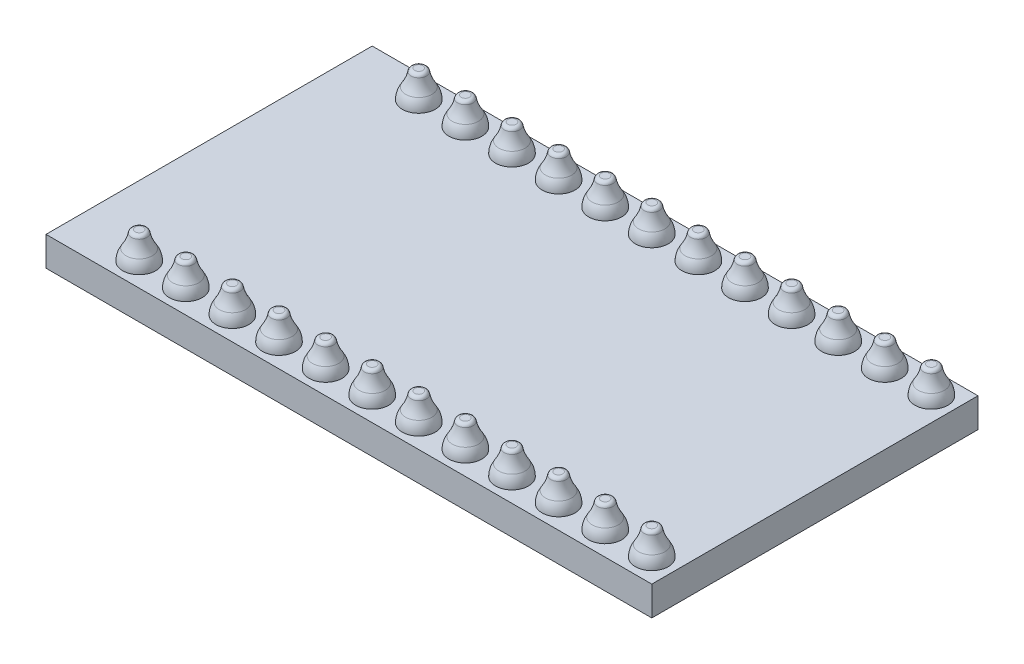
SolidWorks part; units mm, degrees
material "E-Glass Fiber"
ref_plane "Front Plane" through (0, 0, 0) normal (0, 0, 1) x (1, 0, 0)
ref_plane "Top Plane" through (0, 0, 0) normal (0, 1, 0) x (1, 0, 0)
ref_plane "Right Plane" through (0, 0, 0) normal (1, 0, 0) x (0, 0, -1)
sketch "Sketch1" plane through (0, 0, 0) normal (0, 1, 0) x (1, 0, 0)
  line L0 (0, 7.62) -> (-3.81, 7.62) construction
  line L1 (-3.81, 16.51) -> (29.21, 16.51)
  line L2 (-3.81, 16.51) -> (-3.81, -1.27)
  line L3 (-3.81, -1.27) -> (29.21, -1.27)
  line L4 (29.21, 16.51) -> (29.21, -1.27)
  line L5 (0, 0) -> (27.94, 0) construction
  line L6 (0, 0) -> (0, 15.24) construction
  line L7 (0, 15.24) -> (27.94, 15.24) construction
  line L8 (27.94, 0) -> (27.94, 15.24) construction
  line L10 (27.94, 7.62) -> (29.21, 7.62) construction
  dimension "D1" = 33.02
  dimension "D2" = 17.78
  dimension "D3" = 15.24
  dimension "D4" = 27.94
  dimension "D5" = 1.27
extrude "Boss-Extrude2" add sketch "Sketch1" along normal blind 1.6
sketch "Sketch2" plane through (0, 0, 0) normal (0, 1, 0) x (1, 0, 0)
  line L0 (0, -0.88) -> (0, 0.88) construction
  line L2 (-0.88, 0) -> (0.88, 0) construction
  circle A0 centre (0, 0) radius 0.45
  circle A1 centre (0, 15.24) radius 0.45
  dimension "D1" = 0.9
  dimension "D2" = 15.24
extrude "Cut-Extrude2" cut sketch "Sketch2" along normal blind 1.6
pattern_linear "LPattern3" count 12 spacing 2.54 along (1, 0, 0) of "Cut-Extrude2"
sketch "Sketch6" plane through (0, 0, 0) normal (1, 0, 0) x (0, 0, -1)
  line L0 (0, 1.6) -> (0.9, 1.6)
  line L1 (-1.27, 1.6) -> (16.51, 1.6) construction
  line L2 (0.2252, 3.1) -> (0, 3.1)
  line L3 (0, 1.705) -> (0, -1.705) construction
  line L4 (0, 3.1) -> (0, 1.6)
  line L5 (0, 1.3722) -> (0, 3.4408) construction
  arc A0 (0.9, 1.6) -> (0.7139, 2.2122) centre (-0.2, 1.6) ccw
  arc A1 (0.7139, 2.2122) -> (0.4221, 2.9352) centre (2.2924, 3.2697) cw
  arc A2 (0.4221, 2.9352) -> (0.2252, 3.1) centre (0.2252, 2.9) ccw
  point P16 (0.4, 3.1)
  dimension "D4" = 1.1
  dimension "D5" = 1.9
  dimension "D6" = 0.2
  dimension "D1" = 1.5
  dimension "D2" = 0.8
  dimension "D3" = 1.8
revolve "Revolve1" add sketch "Sketch6" angle 360 about L5
pattern_linear "LPattern2" count 2 spacing 15.24 along (0, 0, -1) count 12 spacing 2.54 along (1, 0, 0) of "Revolve1"
ref_plane "Plane3" through (0, 0, -5.08) normal (0, 0, 1) x (1, 0, 0)
sketch "Sketch9" plane through (0, 0, 0) normal (0, 1, 0) x (1, 0, 0)
  line L0 (-1.705, 0) -> (1.705, 0) construction
  line L2 (-3.81, 16.51) -> (-3.81, -1.27) construction
  circle A0 centre (-0.06, 5.725) radius 0.4
  circle A1 centre (-0.06, 9.475) radius 0.4
  dimension "D1" = 0.8
  dimension "D2" = 3.75
  dimension "D3" = 5.725
  dimension "D4" = 3.75
extrude "Cut-Extrude6" [suppressed] cut sketch "Sketch9" along normal blind 10
